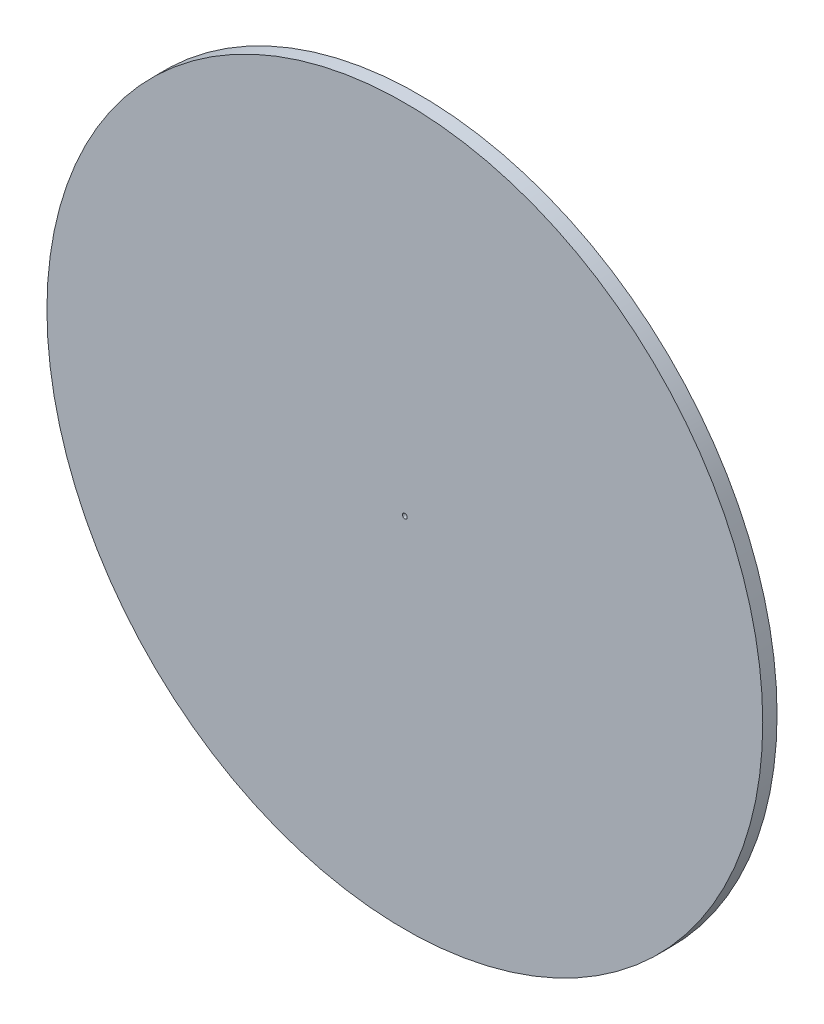
SolidWorks part; units mm, degrees
ref_plane "Alzado" through (0, 0, 0) normal (0, 0, 1) x (1, 0, 0)
ref_plane "Planta" through (0, 0, 0) normal (0, 1, 0) x (1, 0, 0)
ref_plane "Vista lateral" through (0, 0, 0) normal (1, 0, 0) x (0, 0, -1)
sketch "Croquis1" plane through (0, 0, 0) normal (0, 0, 1) x (1, 0, 0)
  circle A0 centre (0, 0) radius 0.5
  circle A1 centre (0, 0) radius 75
  dimension "D1" = 150
  dimension "D2" = 1
extrude "Saliente-Extruir1" add sketch "Croquis1" along normal blind 3
